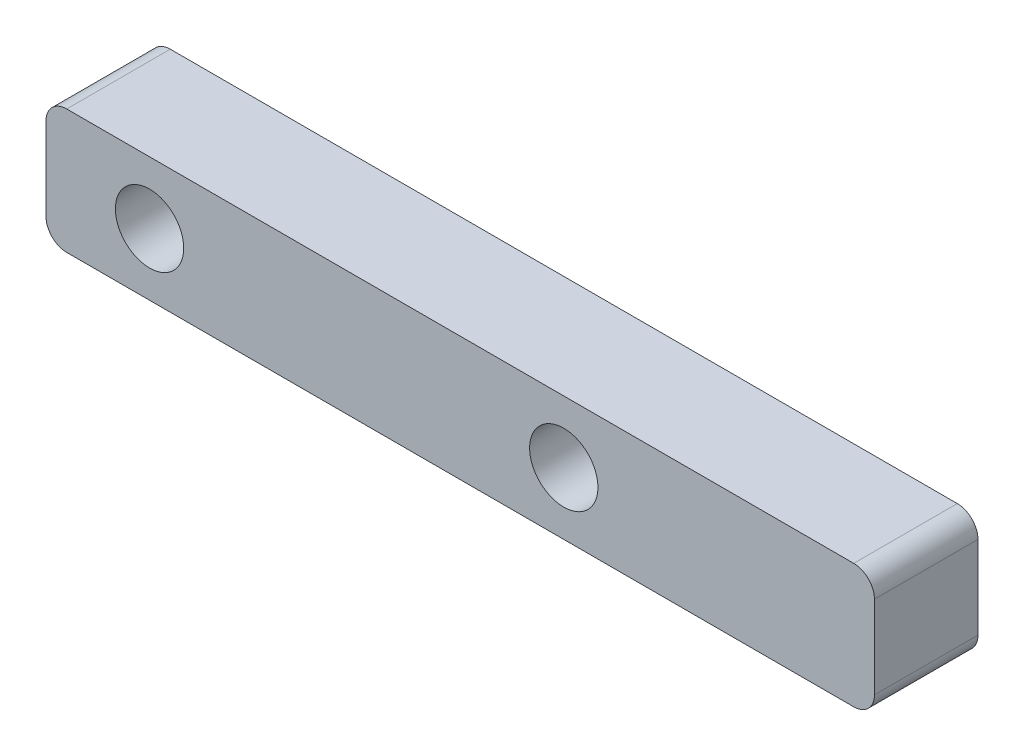
SolidWorks part; units mm, degrees
material "ABS"
ref_plane "前视基准面" through (0, 0, 0) normal (0, 0, 1) x (1, 0, 0)
ref_plane "上视基准面" through (0, 0, 0) normal (0, 1, 0) x (1, 0, 0)
ref_plane "右视基准面" through (0, 0, 0) normal (1, 0, 0) x (0, 0, -1)
other "Configuration Table"
sketch "草图1" plane through (0, 0, 0) normal (0, 0, 1) x (1, 0, 0)
  line L1 (-20, -3) -> (20, -3)
  line L2 (-20, -3) -> (-20, 3)
  line L3 (-20, 3) -> (20, 3)
  line L4 (20, -3) -> (20, 3)
  line L5 (-20, -3) -> (20, 3) construction
  line L6 (-20, 3) -> (20, -3) construction
  point P0 (0, 0)
  dimension "D1" = 40
  dimension "D2" = 6
extrude "凸台-拉伸1" add sketch "草图1" along normal blind 5
sketch "草图2" plane through (0, 0, 5) normal (0, 0, 1) x (1, 0, 0)
  line L0 (-20, 3) -> (-20, -3) construction
  circle A0 centre (5, 0) radius 1.65
  circle A1 centre (-15, 0) radius 1.65
  dimension "D1" = 3.3
  dimension "D3" = 5
  dimension "D2" = 20
extrude "切除-拉伸1" cut sketch "草图2" against normal blind 7
fillet "圆角1" radius 1 4 edges at (20, -3, 2.5) (-20, -3, 2.5) (20, 3, 2.5) (-20, 3, 2.5)
